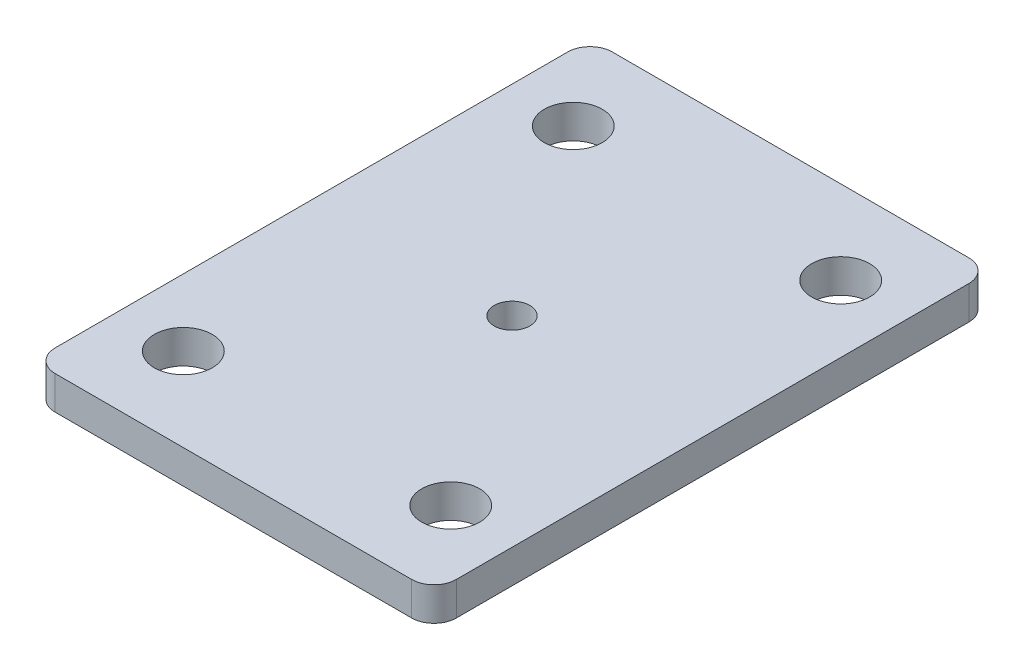
SolidWorks part; units mm, degrees
material "E-玻璃纤维"
ref_plane "前视基准面" through (0, 0, 0) normal (0, 0, 1) x (1, 0, 0)
ref_plane "上视基准面" through (0, 0, 0) normal (0, 1, 0) x (1, 0, 0)
ref_plane "右视基准面" through (0, 0, 0) normal (1, 0, 0) x (0, 0, -1)
sketch "草图1" plane through (0, 0, 0) normal (0, 1, 0) x (1, 0, 0)
  line L1 (-18, 25) -> (18, 25)
  line L2 (-18, 25) -> (-18, -25)
  line L3 (-18, -25) -> (18, -25)
  line L4 (18, 25) -> (18, -25)
  line L5 (-18, 25) -> (18, -25) construction
  line L6 (-18, -25) -> (18, 25) construction
  line L7 (-12, 17.5) -> (12, 17.5) construction
  line L8 (-12, 17.5) -> (-12, -17.5) construction
  line L9 (-12, -17.5) -> (12, -17.5) construction
  line L10 (12, 17.5) -> (12, -17.5) construction
  line L11 (-12, 17.5) -> (12, -17.5) construction
  line L12 (-12, -17.5) -> (12, 17.5) construction
  circle A0 centre (-12, 17.5) radius 2.6
  circle A1 centre (12, 17.5) radius 2.6
  circle A2 centre (-12, -17.5) radius 2.6
  circle A3 centre (12, -17.5) radius 2.6
  point P0 (0, 0)
  point P5 (0, 0)
  dimension "D5" = 5.2
  dimension "D1" = 36
  dimension "D2" = 50
  dimension "D3" = 24
  dimension "D4" = 35
extrude "凸台-拉伸1" add sketch "草图1" along normal blind 3
sketch "草图2" plane through (0, 3, 0) normal (0, 1, 0) x (1, 0, 0)
  circle A0 centre (0, 0) radius 8.05
  dimension "D1" = 16.1
extrude "切除-拉伸1" [suppressed] cut sketch "草图2" against normal blind 45
sketch "草图3" plane through (0, 3, 0) normal (0, 1, 0) x (1, 0, 0)
  line L0 (0, 5.7198) -> (0, 0) construction
  line L1 (0, 0) -> (13.5, 0) construction
  line L2 (9.5, 0) -> (9.5, 6.0299) construction
  line L3 (13.5, 0) -> (13.5, 5.1717) construction
  circle A0 centre (0, 0) radius 9 construction
  circle A1 centre (13.5, 0) radius 1.2
  circle A2 centre (-13.5, 0) radius 1.2
  dimension "D1" = 18
  dimension "D2" = 2.4
  dimension "D3" = 4
  dimension "D4" = 13.5
extrude "切除-拉伸2" [suppressed] cut sketch "草图3" against normal blind 4
sketch "草图4" [suppressed] plane through (0, 4, 0) normal (0, 1, 0) x (1, 0, 0)
  line L0 (0, 30.8354) -> (0, 0) construction
  line L1 (0, 0) -> (31.9649, 0) construction
  line L2 (-12, 17.5) -> (-12, 28.0885) construction
  line L3 (11.85, 25.942) -> (12.15, 25.942)
  line L4 (-11.85, 19.2289) -> (-12.15, 19.2289)
  line L5 (-11.85, 19.2289) -> (-11.85, 25.942)
  line L6 (-11.85, 25.942) -> (-12.15, 25.942)
  line L7 (-12.15, 19.2289) -> (-12.15, 25.942)
  line L8 (12.15, 19.2289) -> (12.15, 25.942)
  line L9 (11.85, 19.2289) -> (12.15, 19.2289)
  line L10 (11.85, 19.2289) -> (11.85, 25.942)
  line L11 (11.85, -19.2289) -> (11.85, -25.942)
  line L12 (11.85, -19.2289) -> (12.15, -19.2289)
  line L13 (12.15, -19.2289) -> (12.15, -25.942)
  line L14 (11.85, -25.942) -> (12.15, -25.942)
  line L15 (-11.85, -25.942) -> (-12.15, -25.942)
  line L16 (-12.15, -19.2289) -> (-12.15, -25.942)
  line L17 (-11.85, -19.2289) -> (-12.15, -19.2289)
  line L18 (-11.85, -19.2289) -> (-11.85, -25.942)
  line L19 (-13.5, 0) -> (-19.9902, 0) construction
  line L20 (12.5483, 0.15) -> (18.9413, 0.15)
  line L21 (-12.5483, -0.15) -> (-18.9413, -0.15)
  line L22 (-12.5483, -0.15) -> (-12.5483, 0.15)
  line L23 (-12.5483, 0.15) -> (-18.9413, 0.15)
  line L24 (-18.9413, -0.15) -> (-18.9413, 0.15)
  line L25 (18.9413, -0.15) -> (18.9413, 0.15)
  line L26 (12.5483, -0.15) -> (18.9413, -0.15)
  line L27 (12.5483, -0.15) -> (12.5483, 0.15)
  dimension "D1" = 0.3
  dimension "D2" = 0.3
extrude "切除-拉伸3" [suppressed] cut sketch "草图4" against normal blind 4
sketch "草图5" plane through (0, 3, 0) normal (0, 1, 0) x (1, 0, 0)
  line L0 (0, 0) -> (0, -25) construction
  line L1 (-18, -25) -> (18, -25) construction
  line L3 (0.15, -27.2772) -> (-0.15, -27.2772)
  line L4 (0.15, -27.2772) -> (0.15, -3.5153)
  line L5 (0.15, -3.5153) -> (-0.15, -3.5153)
  line L6 (-0.15, -27.2772) -> (-0.15, -3.5153)
  dimension "D1" = 0.3
extrude "切除-拉伸4" [suppressed] cut sketch "草图5" against normal blind 4
fillet "圆角1" radius 2 4 edges at (18, 1.5, -25) (-18, 1.5, -25) (-18, 1.5, 25) (18, 1.5, 25)
sketch "草图6" plane through (0, 3, 0) normal (0, 1, 0) x (1, 0, 0)
  line L0 (18, 0) -> (-18, 0) construction
  line L1 (18, -23) -> (18, 23) construction
  line L2 (-18, 23) -> (-18, -23) construction
  line L3 (0, 0) -> (0, -25) construction
  line L4 (-16, -25) -> (16, -25) construction
  circle A2 centre (0, 0) radius 1.6
  dimension "D1" = 3.2
extrude "切除-拉伸5" cut sketch "草图6" against normal blind 10
